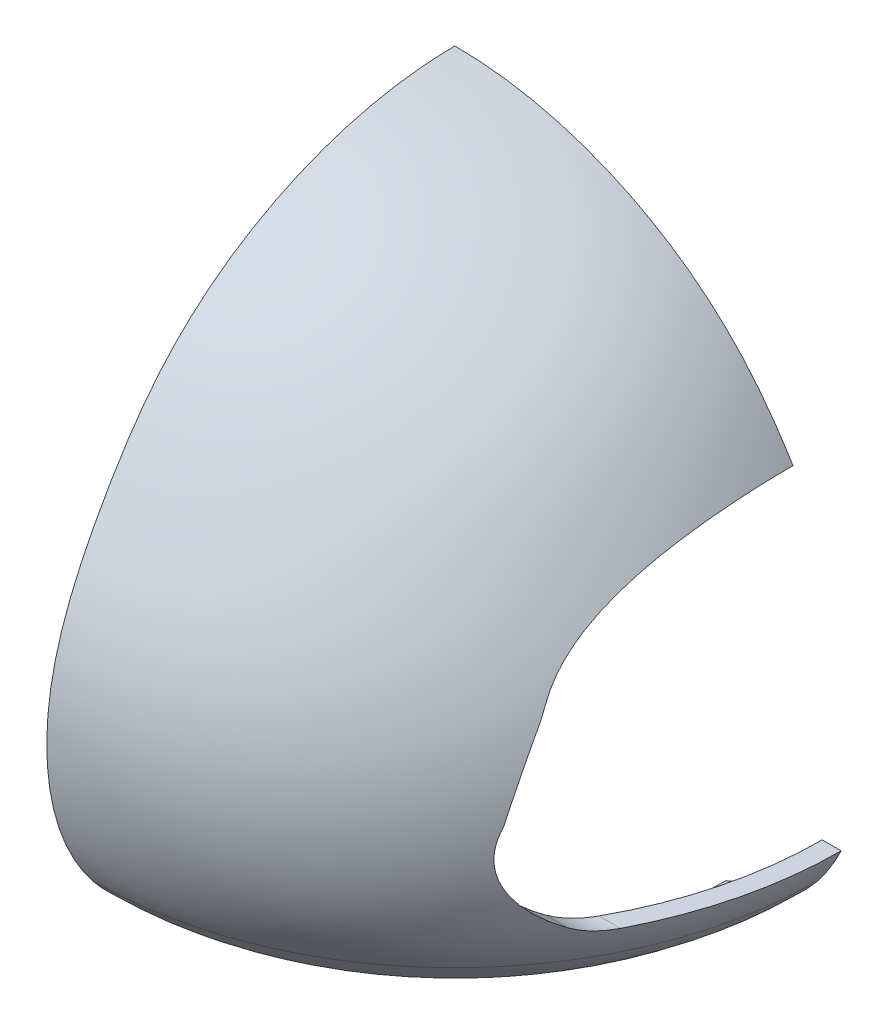
SolidWorks part; units mm, degrees
ref_plane "Front Plane" through (0, 0, 0) normal (0, 0, 1) x (1, 0, 0)
ref_plane "Top Plane" through (0, 0, 0) normal (0, 1, 0) x (1, 0, 0)
ref_plane "Right Plane" through (0, 0, 0) normal (1, 0, 0) x (0, 0, -1)
sketch "Sketch3" plane through (0, 0, 0) normal (0, 0, 1) x (1, 0, 0)
  line L0 (0.0245, 157.0849) -> (0.0245, 152.0849)
  line L1 (0.0245, -20.9434) -> (0.0245, -25.9434)
  line L2 (0.0245, 171.6103) -> (0.0245, -40.6784) construction
  spline S0 degree 3 poles (-103.1746, 0) (-78.8328, -30.0641) (-33.4587, -20.9434) (0.0245, -20.9434) knots 0 0 0 0 1 1 1 1
  spline S1 degree 3 poles (-103.1746, 0) (-114.7602, 14.5762) (-119.8367, 49.2728) (-101.4518, 88.6739) (-71.3798, 134.4794) (-29.75, 152.0849) (0.0245, 152.0849) knots 0 0 0 0 0.250738 0.442513 0.587645 1 1 1 1
  spline S2 degree 1 poles (-107.0747, -3.1288) (0.0245, -25.9434) knots 0 0 1 1 construction
  spline S3 degree 1 poles (-107.0747, -3.1288) (0.0245, 157.0849) knots 0 0 1 1 construction
  spline S4 degree 3 poles (0.0245, -25.9434) (-1.0078, -25.9434) (-3.0527, -25.9607) (-7.3007, -26.054) (-12.7748, -26.2598) (-19.5869, -26.581) (-28.9113, -27.0143) (-40.9004, -27.387) (-55.4438, -26.9753) (-69.7899, -25.0863) (-81.2787, -21.7225) (-89.9598, -17.6028) (-96.1383, -13.7178) (-100.9459, -9.7522) (-104.5344, -6.1303) (-106.2545, -4.1419) (-107.0747, -3.1288) knots -0.000194 -0.000194 -0.000194 -0.000194 0.031062 0.062318 0.12483 0.187342 0.249854 0.374879 0.499903 0.624927 0.749951 0.812464 0.874976 0.937488 0.968744 1 1 1 1
  spline S5 degree 3 poles (-107.0747, -3.1288) (-107.8617, -2.1388) (-109.3756, -0.1005) (-112.0955, 4.1156) (-114.956, 9.6441) (-117.5537, 16.5853) (-119.9627, 26.1346) (-121.1031, 38.4065) (-119.7936, 53.0884) (-116.0899, 67.0475) (-110.6339, 80.233) (-104.0343, 92.719) (-96.8153, 104.7516) (-88.5122, 116.2468) (-78.6677, 126.6978) (-67.4647, 135.7136) (-55.1826, 143.2806) (-42.0542, 149.311) (-28.3211, 153.7314) (-14.2042, 156.4574) (-4.7225, 157.0849) (0.0245, 157.0849) knots -0.000101 -0.000101 -0.000101 -0.000101 0.015525 0.031152 0.062405 0.093658 0.124911 0.187418 0.249924 0.31243 0.374937 0.437443 0.499949 0.562456 0.624962 0.687468 0.749975 0.812481 0.874987 0.937494 1 1 1 1
  dimension "D1" = 5
revolve "Revolve5" add sketch "Sketch3" angle 360 about L2
ref_plane "Plane2" through (0, -30, 0) normal (0, 1, 0) x (1, 0, 0)
sketch "Sketch4" plane through (0, -30, 0) normal (0, 1, 0) x (1, 0, 0)
  circle A0 centre (0, 0) radius 80.1001
extrude "Cut-Extrude2" cut sketch "Sketch4" along normal blind 20
sketch "Sketch5" plane through (0, 0, 0) normal (1, 0, 0) x (0, 0, -1)
  line L0 (-52.4765, 8.1366) -> (52.4765, 8.1366)
  arc A0 (-52.4765, 8.1366) -> (-63.3365, 11.3419) centre (-52.4765, 28.1366) cw
  arc A1 (52.4765, 8.1366) -> (63.3365, 11.3419) centre (52.4765, 28.1366) ccw
  arc A2 (-69.3418, 64.1464) -> (-67.0221, 68.7237) centre (-184.1186, 125.1898) ccw
  arc A3 (70.4941, 63.0471) -> (66.203, 70.3101) centre (188.8284, 137.8602) cw
  arc A4 (78.7462, 39.318) -> (77.2009, 46.2401) centre (214.5664, 73.272) cw
  ellipse E0 centre (0, 56.3684) end of major axis (69.9377, 56.3684) minor radius 43.2422 (66.203, 70.3101) -> (-67.0221, 68.7237) ccw
  ellipse E1 centre (0, 34.6362) end of major axis (79.3292, 34.6362) minor radius 38.6866 (-77.8366, 42.1057) -> (-63.3365, 11.3419) ccw
  ellipse E2 centre (0, 34.6362) end of major axis (79.3292, 34.6362) minor radius 38.6866 (63.3365, 11.3419) -> (78.7462, 39.318) ccw
  spline S0 degree 3 poles (-69.3418, 64.1464) (-73.0617, 57.1522) (-75.8989, 49.7908) (-77.8366, 42.1057) knots 0.114274 0.114274 0.114274 0.114274 1 1 1 1
  spline S1 degree 3 poles (70.4941, 63.0471) (72.3563, 60.1016) (75.0451, 54.6733) (76.6927, 48.8224) (77.2009, 46.2401) knots 0.168182 0.168182 0.168182 0.168182 0.552819 0.845618 0.845618 0.845618 0.845618
  dimension "D1" = 20
  dimension "D2" = 130
  dimension "D3" = 140
  dimension "D4" = 140
extrude "Cut-Extrude3" cut sketch "Sketch5" along normal through all
scale "Scale2" bodies to scale 106 scale about centroid uniform scaling yes scale factor 1
ref_plane "Plane3" through (0, 105, 0) normal (0, 1, 0) x (1, 0, 0)
sketch "Sketch6" plane through (0, 105, 0) normal (0, 1, 0) x (1, 0, 0)
  circle A0 centre (0, 0) radius 10
extrude "Boss-Extrude1" add sketch "Sketch6" against normal up to surface (46.603 mm away)
sketch "Sketch7" plane through (0, 0, 0) normal (0, 0, 1) x (1, 0, 0)
  line L1 (174.4564, -182.2964) -> (-174.4564, -182.2964)
  line L2 (174.4564, -182.2964) -> (174.4564, 182.2964)
  line L3 (174.4564, 182.2964) -> (-174.4564, 182.2964)
  line L4 (-174.4564, -182.2964) -> (-174.4564, 182.2964)
  line L5 (174.4564, -182.2964) -> (-174.4564, 182.2964) construction
  line L6 (174.4564, 182.2964) -> (-174.4564, -182.2964) construction
  point P0 (0, 0)
extrude "Cut-Extrude4" cut sketch "Sketch7" against normal blind 159
ref_plane "Plane4" through (0, 0, 0) normal (1, 0, 0) x (0, 0, -1)
sketch "Sketch10" plane through (0, 0, 0) normal (1, 0, 0) x (0, 0, -1)
  line L1 (160.9257, -168.0535) -> (-160.9257, -168.0535)
  line L2 (160.9257, -168.0535) -> (160.9257, 168.0534)
  line L3 (160.9257, 168.0534) -> (-160.9257, 168.0534)
  line L4 (-160.9257, -168.0535) -> (-160.9257, 168.0534)
  line L5 (160.9257, -168.0535) -> (-160.9257, 168.0534) construction
  line L6 (160.9257, 168.0534) -> (-160.9257, -168.0535) construction
  point P0 (0, 0)
extrude "Cut-Extrude5" cut sketch "Sketch10" against normal blind 200
